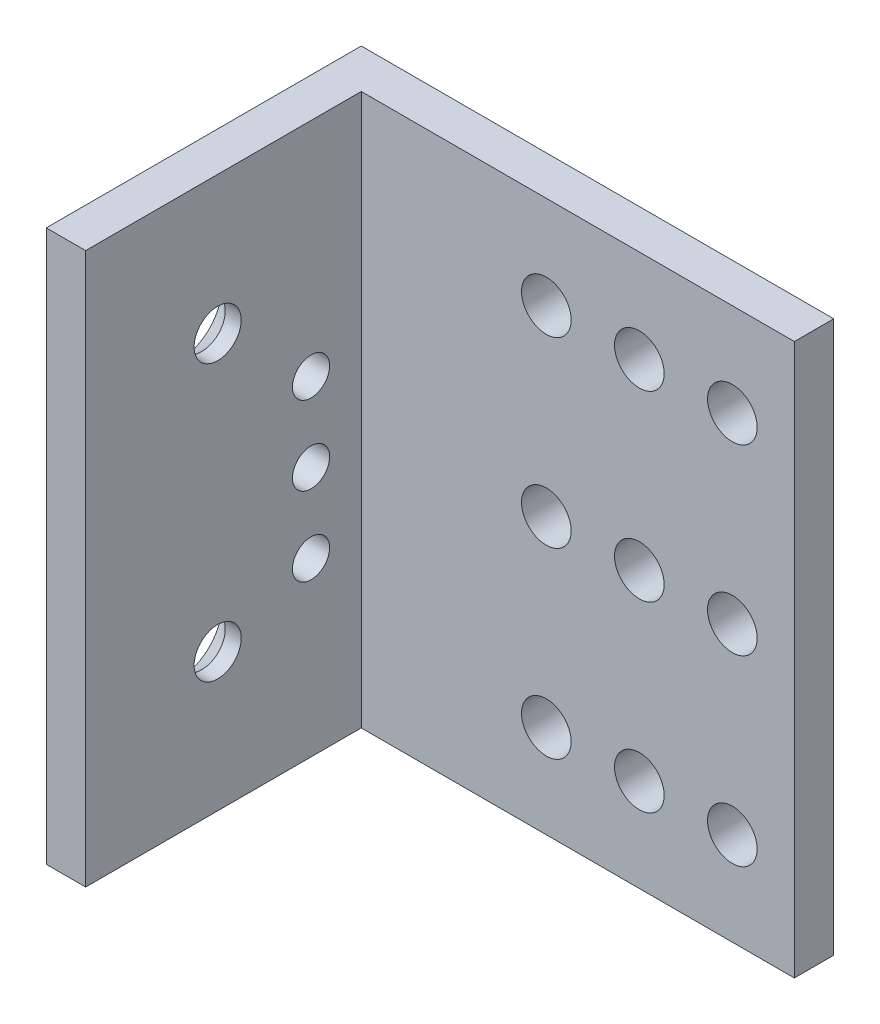
SolidWorks part; units mm, degrees
ref_plane "Front" through (0, 0, 0) normal (0, 0, 1) x (1, 0, 0)
ref_plane "Top" through (0, 0, 0) normal (0, 1, 0) x (1, 0, 0)
ref_plane "Right" through (0, 0, 0) normal (1, 0, 0) x (0, 0, -1)
sketch "Sketch1" plane through (0, 0, 0) normal (0, 1, 0) x (1, 0, 0)
  line L0 (-19.05, -12.7) -> (-15.875, -12.7)
  line L1 (-19.05, -12.7) -> (19.05, -12.7) construction
  line L2 (-19.05, -12.7) -> (-19.05, 12.7)
  line L3 (-19.05, 12.7) -> (19.05, 12.7)
  line L4 (19.05, -12.7) -> (19.05, 12.7) construction
  line L5 (-19.05, -12.7) -> (19.05, 12.7) construction
  line L6 (-19.05, 12.7) -> (19.05, -12.7) construction
  line L7 (-15.875, -12.7) -> (-15.875, 9.525)
  line L8 (-15.875, 9.525) -> (19.05, 9.525)
  line L9 (19.05, 9.525) -> (19.05, 12.7)
  point P0 (0, 0)
  point P10 (0, -12.7)
  dimension "D1" = 38.1
  dimension "D2" = 25.4
  dimension "D3" = 34.925
  dimension "D4" = 22.225
extrude "Boss-Extrude1" add sketch "Sketch1" along normal mid plane 44.45
sketch "Sketch2" plane through (-19.05, 0, 0) normal (-1, 0, 0) x (0, 0, 1)
  line L0 (-9.525, 22.225) -> (-9.525, -22.225) construction
  line L1 (-12.7, 22.225) -> (12.7, 22.225) construction
  line L2 (-12.7, -22.225) -> (12.7, -22.225) construction
  line L3 (12.7, 22.225) -> (12.7, -22.225) construction
  line L4 (-9.525, 22.225) -> (12.7, 22.225) construction
  line L5 (-9.525, 22.225) -> (-9.525, 0) construction
  line L6 (-9.525, 0) -> (12.7, 0) construction
  line L7 (12.7, 22.225) -> (12.7, 0) construction
  line L9 (-4.445, 22.225) -> (-4.445, -22.225) construction
  circle A0 centre (2.055, 11.1125) radius 2
  point P14 (12.7, 11.1125)
  dimension "D1" = 4
  dimension "D2" = 5.08
  dimension "D3" = 6.5
extrude "Cut-Extrude1" [suppressed] cut sketch "Sketch2" against normal through all
hole_wizard "CSK for #6 Flat Head Machine Screw1" positions "Sketch3" profile "Sketch5" countersink size "#6" standard "ANSI Inch" end condition through all
sketch "Sketch3" plane through (-19.05, 0, 0) normal (-1, 0, 0) x (0, 0, 1)
  point P0 (2.055, 11.1125)
sketch "Sketch5" plane through (-19.05, 11.1125, 2.055) normal (0, 1, 0) x (0, 0, 1)
  line L0 (0, 0) -> (0, 38.1)
  line L1 (0, 38.1) -> (1.8986, 38.1)
  line L2 (1.8986, 38.1) -> (1.8986, 1.892)
  line L3 (1.8986, 1.892) -> (3.5433, 0)
  line L5 (3.5433, 0) -> (0, 0)
  line L6 (-1.8986, 1.892) -> (-3.5433, 0) construction
  line L11 (0, -6.35) -> (0, 107.95) construction
  dimension "Thru Hole Dia." = 3.7973
  dimension "Thru Hole Depth" = 38.1
  dimension "Near C'Sink Dia." = 7.0866
  dimension "Near C'Sink Angle" = 82
sketch "Sketch6" plane through (0, 0, -12.7) normal (0, 0, -1) x (-1, 0, 0)
  line L0 (-19.05, 22.225) -> (-19.05, -22.225) construction
  line L1 (-19.05, -22.225) -> (19.05, -22.225) construction
  line L2 (-14.05, -14.725) -> (-6.55, -14.725) construction
  circle A0 centre (-14.05, -14.725) radius 2
  circle A1 centre (-6.55, -14.725) radius 2
  circle A2 centre (-6.55, 0) radius 2
  circle A3 centre (-6.55, 14.725) radius 2
  circle A4 centre (-14.05, 0) radius 2
  circle A5 centre (-14.05, 14.725) radius 2
  circle A6 centre (0.95, -14.725) radius 2
  circle A7 centre (0.95, 0) radius 2
  circle A8 centre (0.95, 14.725) radius 2
  point P7 (-14.05, 0)
  dimension "D4" = 4
  dimension "D1" = 5
  dimension "D2" = 7.5
  dimension "D3" = 14.725
  dimension "D8" = 7.5
  dimension "D5" = 3
  dimension "D6" = 3
extrude "Cut-Extrude2" cut sketch "Sketch6" against normal through all
mirror "Mirror1" about plane through (0, 0, 0) normal (0, 1, 0) of "CSK for #6 Flat Head Machine Screw1"
sketch "Sketch7" plane through (-15.875, 0, 0) normal (1, 0, 0) x (0, 0, -1)
  line L0 (9.525, 22.225) -> (9.525, -22.225) construction
  line L1 (5.475, -8.35) -> (5.475, 4.35) construction
  circle A0 centre (5.475, -2) radius 1.5
  circle A1 centre (5.475, -8.35) radius 1.5
  circle A2 centre (5.475, 4.35) radius 1.5
  point P9 (0, 0)
  point P10 (5.475, -2)
  dimension "D2" = 3
  dimension "D1" = 4.05
  dimension "D3" = 2
  dimension "D4" = 6.35
extrude "Cut-Extrude3" cut sketch "Sketch7" against normal through all
